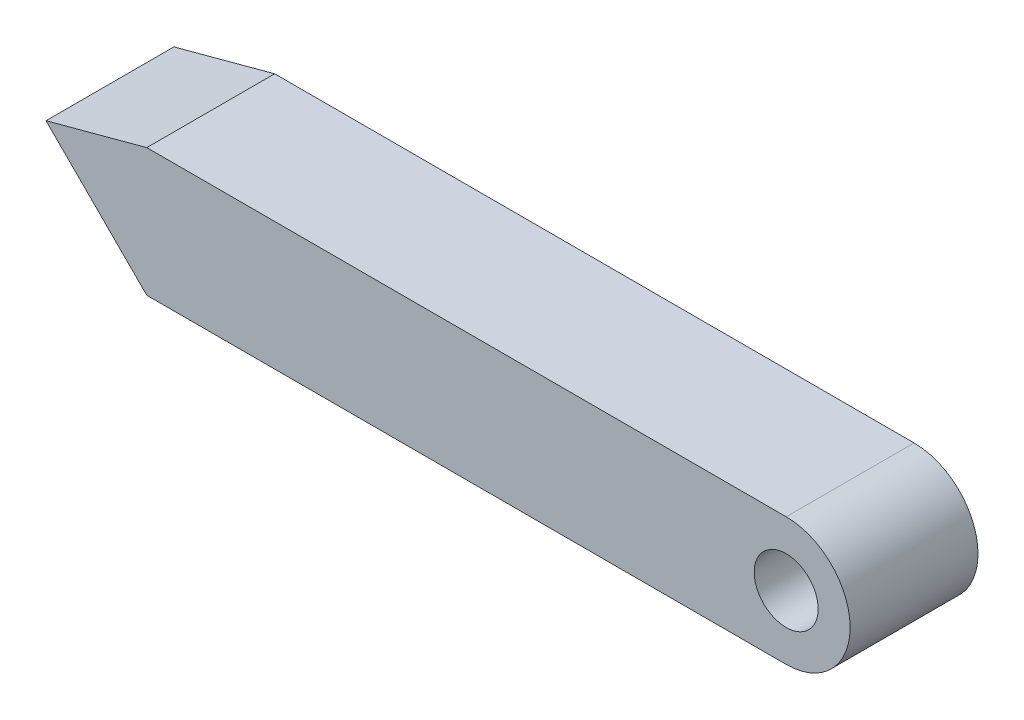
SolidWorks part; units mm, degrees
ref_plane "Front Plane" through (0, 0, 0) normal (0, 0, 1) x (1, 0, 0)
ref_plane "Top Plane" through (0, 0, 0) normal (0, 1, 0) x (1, 0, 0)
ref_plane "Right Plane" through (0, 0, 0) normal (1, 0, 0) x (0, 0, -1)
sketch "Sketch1" plane through (0, 0, 0) normal (0, 0, 1) x (1, 0, 0)
  line L0 (0, 5) -> (-50, 5)
  line L1 (-50, 5) -> (-57.8805, 2.8805)
  line L2 (0, -5) -> (-50, -5)
  line L4 (-50, -5) -> (-57.8805, 2.8805)
  circle A0 centre (0, 0) radius 2.5
  arc A1 (0, -5) -> (0, 5) centre (0, 0) ccw
  point P3 (0, 5)
  point P4 (0, 2.5)
  dimension "D1" = 2.5
  dimension "D3" = 5
  dimension "D2" = 50
extrude "Boss-Extrude1" add sketch "Sketch1" along normal blind 10
